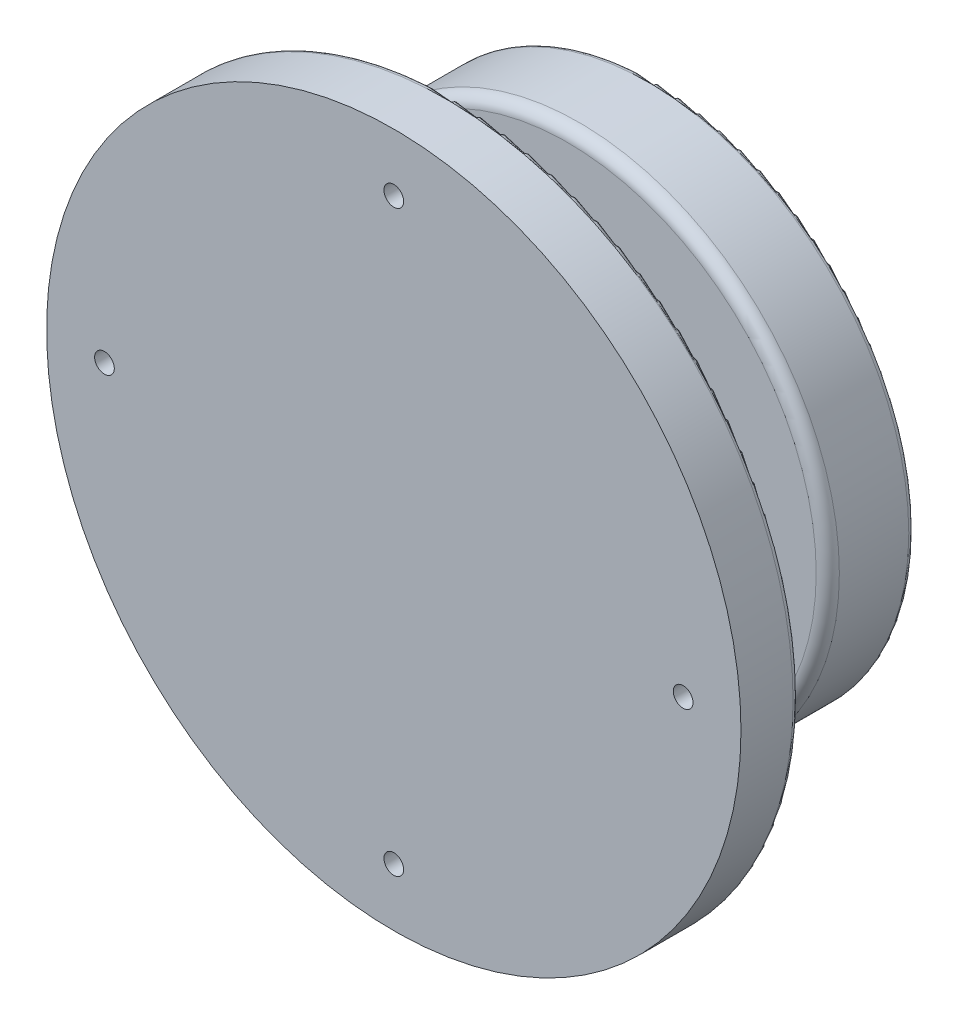
SolidWorks part; units mm, degrees
material "ABS PC"
ref_plane "Plan de face" through (0, 0, 0) normal (0, 0, 1) x (1, 0, 0)
ref_plane "Plan de dessus" through (0, 0, 0) normal (0, 1, 0) x (1, 0, 0)
ref_plane "Plan de droite" through (0, 0, 0) normal (1, 0, 0) x (0, 0, -1)
sketch "Esquisse1" plane through (0, 0, 0) normal (0, 0, 1) x (1, 0, 0)
  circle A0 centre (0, 0) radius 45
  dimension "D1" = 90
extrude "Boss.-Extru.1" add sketch "Esquisse1" along normal blind 15
sketch "Esquisse3" plane through (0, 0, 15) normal (0, 0, 1) x (1, 0, 0)
  circle A0 centre (0, 0) radius 10
  dimension "D1" = 20
extrude "Boss.-Extru.2" add sketch "Esquisse3" along normal blind 20
sketch "Esquisse4" plane through (0, 0, 35) normal (0, 0, 1) x (1, 0, 0)
  circle A0 centre (0, 0) radius 60
  dimension "D1" = 120
extrude "Boss.-Extru.3" add sketch "Esquisse4" along normal blind 10
fillet "Congé1" radius 2 1 edges at (45, 0, 15)
sketch "Esquisse5" plane through (0, 0, 0) normal (0, 0, -1) x (-1, 0, 0)
  line L1 (-11.6, -2) -> (11.6, -2)
  line L2 (-11.6, -2) -> (-11.6, -33.8)
  line L3 (-11.6, -33.8) -> (11.6, -33.8)
  line L4 (11.6, -2) -> (11.6, -33.8)
  line L5 (-11.6, -2) -> (-11.6, 5.5)
  line L6 (11.6, -2) -> (11.6, 5.5)
  line L7 (-7.1, 10) -> (7.1, 10)
  arc A0 (-11.6, 5.5) -> (-7.1, 10) centre (-7.1, 5.5) cw
  arc A1 (7.1, 10) -> (11.6, 5.5) centre (7.1, 5.5) cw
  circle A2 centre (0, 0) radius 2.15
  dimension "D3" = 4.3
  dimension "D6" = 4.5
  dimension "D7" = 4.5
  dimension "D1" = 2
  dimension "D2" = 11.6
  dimension "D4" = 43.8
  dimension "D5" = 23.2
  dimension "D8" = 12
fillet "Congé2" radius 1 1 edges at (60, 0, 35)
fillet "Congé3" radius 1 1 edges at (45, 0, 0)
sketch "Esquisse6" plane through (0, 0, 0) normal (0, 0, 1) x (1, 0, 0)
  circle A0 centre (0, 0) radius 7
  circle A1 centre (7, 0) radius 1.25
  circle A2 centre (-7, 0) radius 1.25
  dimension "D1" = 14
  dimension "D2" = 2.5
hole_wizard "Trou taraudé M31" positions "Esquisse3D1" profile "Esquisse7" tap size "M3" standard "Iso"
sketch3d "Esquisse3D1"
  point P0 (-7, 0, 0)
  point P3 (7, 0, 0)
sketch "Esquisse7" plane through (-7, 0, 0) normal (1, 0, 0) x (0, 1, 0)
  line L0 (0, 0) -> (0, 13.2511)
  line L1 (0, 13.2511) -> (1.25, 12.5)
  line L2 (1.25, 12.5) -> (1.25, 0)
  line L5 (1.25, 0) -> (0, 0)
  line L10 (0, 13.2511) -> (-1.25, 12.5) construction
  line L11 (0, -6.35) -> (0, 107.95) construction
  dimension "Diamètre du trou pour taraudage" = 2.5
  dimension "Profondeur du trou pour taraudage" = 12.5
  dimension "Angle de pointe" = 118
cosmetic thread "Filetage de perçage1" parameters "D1"=10, "D2"=3
cosmetic thread "Filetage de perçage2" parameters "D1"=10, "D2"=3
sketch "Esquisse8" plane through (0, 0, 35) normal (0, 0, 1) x (1, 0, 0)
  circle A0 centre (0, 0) radius 50
  circle A1 centre (0, 50) radius 1.5
  circle A2 centre (50, 0) radius 1.5
  circle A3 centre (0, -50) radius 1.5
  circle A4 centre (-50, 0) radius 1.5
  dimension "D1" = 100
  dimension "D2" = 3
hole_wizard "Chambrage pour vis à tête hexagonale M31" positions "Esquisse3D2" profile "Esquisse9" counterbore size "M3" standard "Iso" end condition through all
sketch3d "Esquisse3D2"
  point P0 (0, 50, 35)
  point P3 (50, 0, 35)
  point P6 (0, -50, 35)
  point P9 (-50, 0, 35)
sketch "Esquisse9" plane through (0, 50, 35) normal (1, 0, 0) x (0, 1, 0)
  line L0 (0, 0) -> (0, 10)
  line L1 (0, 10) -> (1.7, 10)
  line L3 (1.7, 10) -> (1.7, 5)
  line L4 (4.6755, 5) -> (1.7, 5)
  line L5 (4.6755, 5) -> (4.6755, 0.025)
  line L6 (4.6755, 0.025) -> (4.7005, 0)
  line L7 (4.7005, 0) -> (0, 0)
  line L8 (-4.6755, 0.025) -> (-4.7005, 0) construction
  line L11 (0, -6.35) -> (0, 107.95) construction
  dimension "Diamètre du perçage jusqu'au prochain" = 3.4
  dimension "Profondeur du perçage jusqu'au prochain" = 10
  dimension "Diamètre du chambrage" = 9.351
  dimension "Profondeur du chambrage" = 5
  dimension "Diamètre du fraisage entrant" = 9.401
  dimension "Angle du fraisage entrant" = 90
